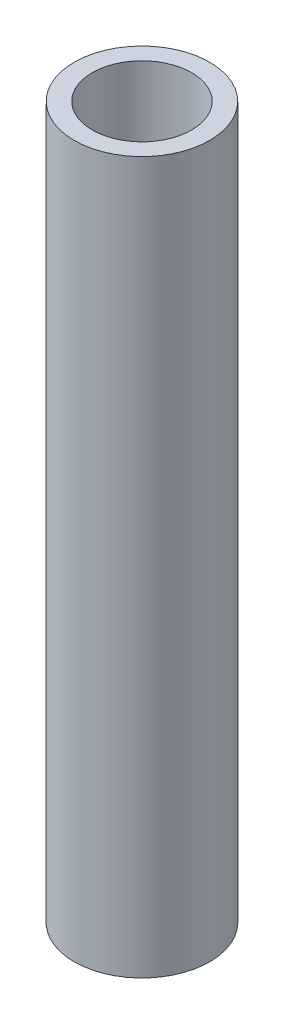
SolidWorks part; units mm, degrees
ref_plane "Front Plane" through (0, 0, 0) normal (0, 0, 1) x (1, 0, 0)
ref_plane "Top Plane" through (0, 0, 0) normal (0, 1, 0) x (1, 0, 0)
ref_plane "Right Plane" through (0, 0, 0) normal (1, 0, 0) x (0, 0, -1)
sketch "Sketch1" plane through (0, 0, 0) normal (0, 1, 0) x (1, 0, 0)
  circle A0 centre (0, 0) radius 15
  circle A1 centre (0, 0) radius 11
  dimension "D1" = 30
  dimension "D2" = 4
extrude "Boss-Extrude1" add sketch "Sketch1" along normal blind 157.5
